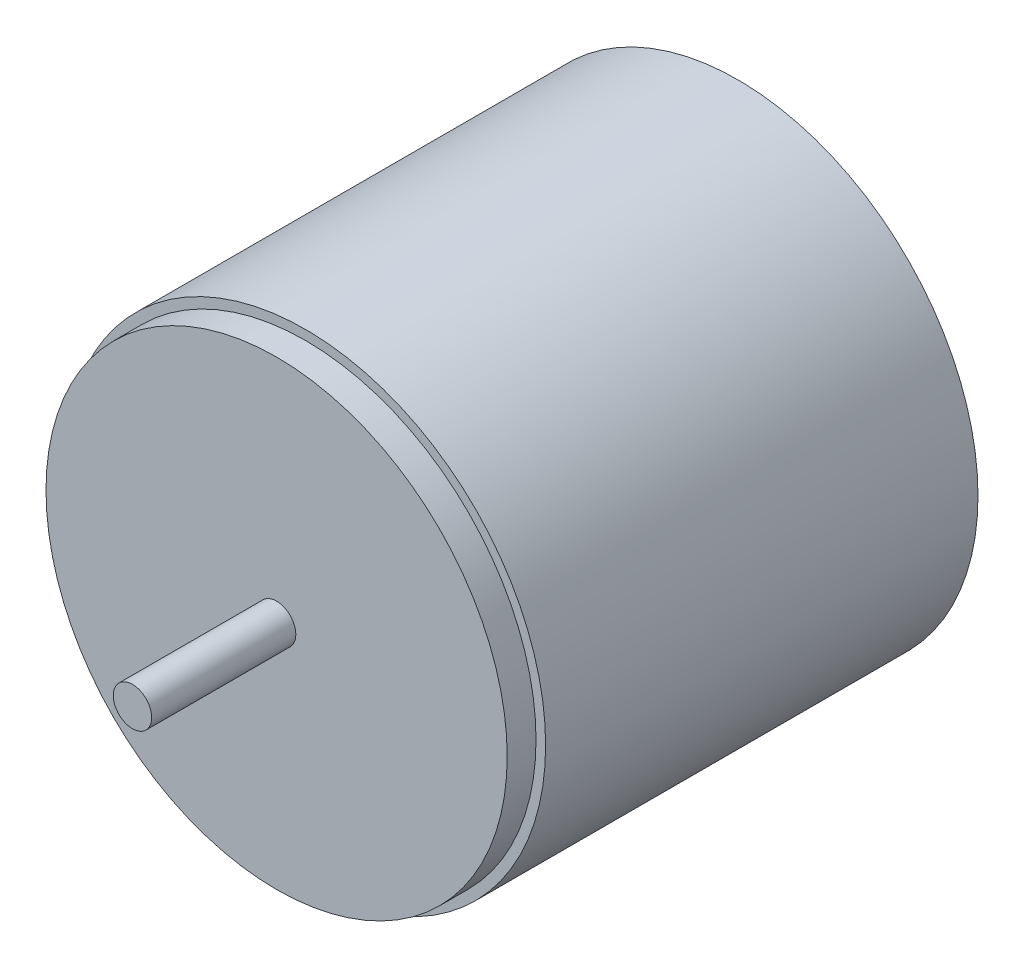
SolidWorks part; units mm, degrees
ref_plane "Front Plane" through (0, 0, 0) normal (0, 0, 1) x (1, 0, 0)
ref_plane "Top Plane" through (0, 0, 0) normal (0, 1, 0) x (1, 0, 0)
ref_plane "Right Plane" through (0, 0, 0) normal (1, 0, 0) x (0, 0, -1)
sketch "Sketch1" plane through (0, 0, 0) normal (0, 0, 1) x (1, 0, 0)
  circle A0 centre (0, 0) radius 25
extrude "Boss-Extrude1" add sketch "Sketch1" along normal blind 45
sketch "Sketch2" plane through (0, 0, 0) normal (0, 0, 1) x (1, 0, 0)
  circle A0 centre (0, 0) radius 24
extrude "Boss-Extrude2" add sketch "Sketch2" along normal blind 48
sketch "Sketch3" plane through (0, 0, 0) normal (0, 0, 1) x (1, 0, 0)
  circle A0 centre (0, 0) radius 2
extrude "Boss-Extrude3" add sketch "Sketch3" along normal blind 63
